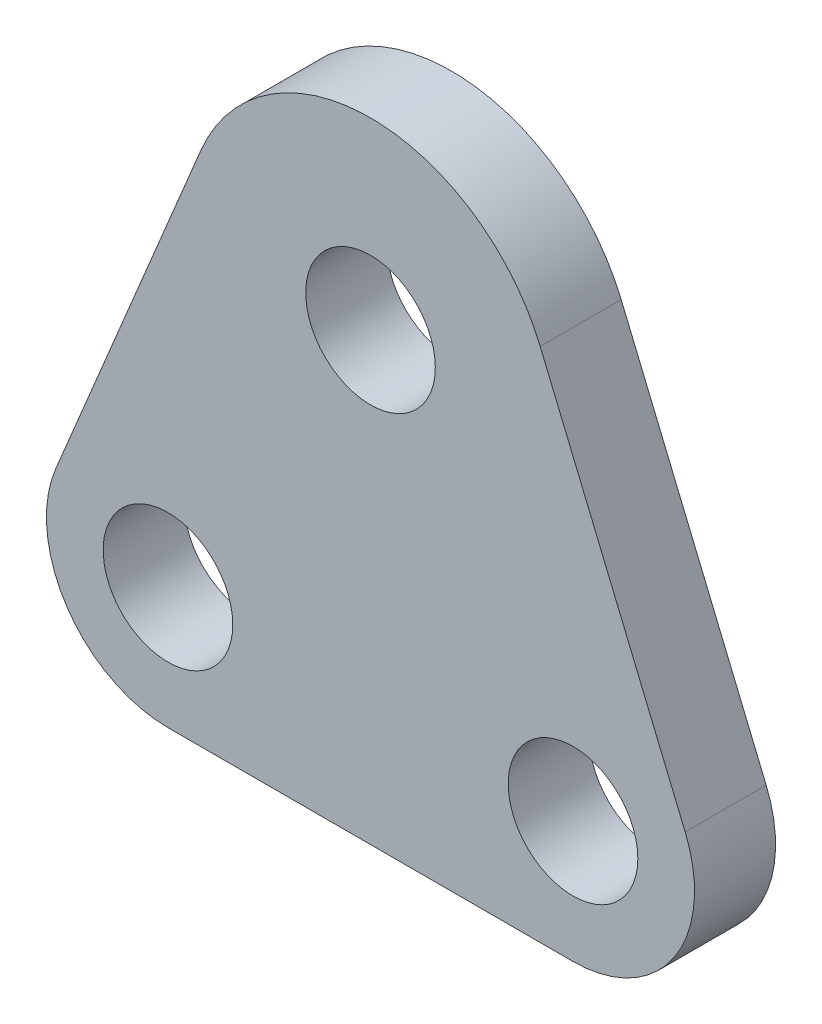
SolidWorks part; units mm, degrees
ref_plane "Front Plane" through (0, 0, 0) normal (0, 0, 1) x (1, 0, 0)
ref_plane "Top Plane" through (0, 0, 0) normal (0, 1, 0) x (1, 0, 0)
ref_plane "Right Plane" through (0, 0, 0) normal (1, 0, 0) x (0, 0, -1)
sketch "Sketch1" plane through (0, 0, 0) normal (0, 0, 1) x (1, 0, 0)
  line L0 (0, 0) -> (10, 0)
  line L1 (0, -3) -> (10, -3)
  line L2 (5, 8) -> (5, 0)
  line L7 (0.8106, 9.7456) -> (-2.7692, 1.1538)
  line L8 (9.1893, 9.7456) -> (12.7692, 1.1538)
  circle A0 centre (10, 0) radius 1.6
  circle A1 centre (0, 0) radius 1.6
  arc A12 (9.1893, 9.7456) -> (0.8106, 9.7456) centre (5, 8) ccw
  circle A13 centre (5, 8) radius 1.6
  arc A14 (10, -3) -> (12.7692, 1.1538) centre (10, 0) ccw
  arc A15 (-2.7692, 1.1538) -> (0, -3) centre (0, 0) ccw
extrude "Boss-Extrude2" add sketch "Sketch1" along normal blind 2
